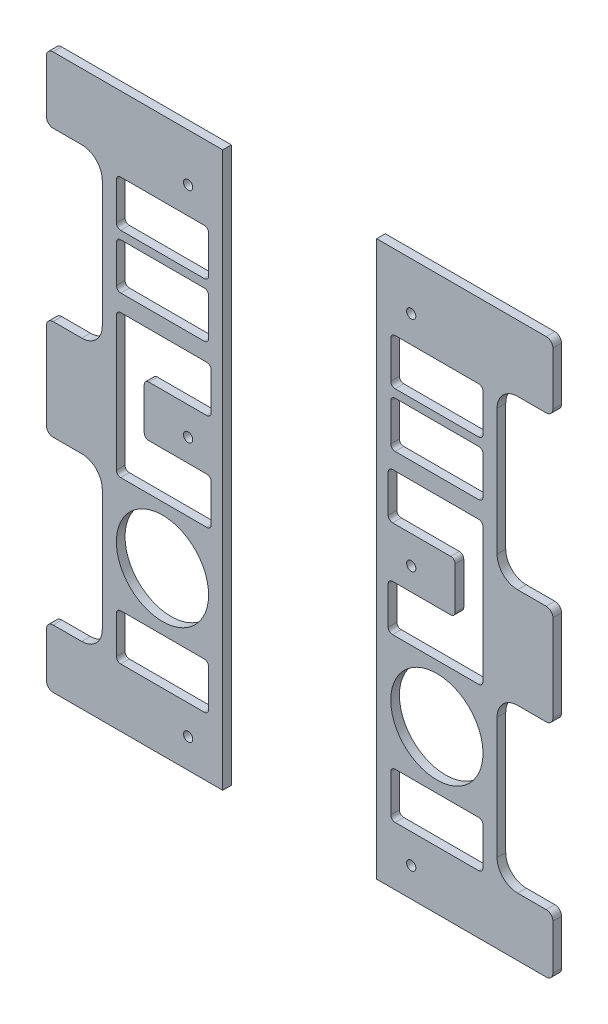
SolidWorks part; units mm, degrees
material "Acrylic (Medium-high impact)"
ref_plane "Front Plane" through (0, 0, 0) normal (0, 0, 1) x (1, 0, 0)
ref_plane "Top Plane" through (0, 0, 0) normal (0, 1, 0) x (1, 0, 0)
ref_plane "Right Plane" through (0, 0, 0) normal (1, 0, 0) x (0, 0, -1)
sketch "Sketch2" plane through (0, 0, 0) normal (0, 0, 1) x (1, 0, 0)
  line L1 (84.7976, -24.2496) -> (218.4211, -24.2496)
  line L2 (84.7976, -24.2496) -> (84.7976, -46.0935)
  line L4 (217.5275, -119.6519) -> (217.5275, -258.9871)
  line L7 (84.7976, -298.45) -> (84.7976, -342.4551)
  line L10 (84.7976, -46.0935) -> (84.7976, -298.45)
  line L11 (84.7976, -172.2717) -> (217.5275, -172.2717) construction
  line L13 (84.7976, -635.4166) -> (271.6317, -635.4166)
  line L14 (84.7976, -635.4166) -> (84.7976, -571.0484)
  line L17 (217.5275, -414.483) -> (217.5275, -548.4457)
  line L18 (84.7976, -342.4551) -> (84.7976, -571.0484)
  line L19 (151.1625, -172.2717) -> (151.1625, -456.7517) construction
  line L24 (84.7976, -456.7517) -> (151.1625, -456.7517) construction
  line L31 (278.9977, -628.0506) -> (278.9977, -578.4177)
  line L33 (278.9977, -606.7976) -> (278.9977, -675.1407) construction
  line L37 (278.9977, -288.878) -> (278.9977, -384.5922)
  line L38 (218.4211, -24.2496) -> (271.6723, -24.2496)
  line L40 (240.0929, -281.5526) -> (271.6723, -281.5526)
  line L41 (240.0929, -97.0864) -> (271.6723, -97.0864)
  line L42 (240.0929, -391.9176) -> (271.6723, -391.9176)
  line L43 (278.9977, -31.575) -> (278.9977, -89.761)
  line L45 (171.2551, -291.3572) -> (171.2551, -337.6663)
  line L47 (201.9625, -317.5) -> (201.9625, -357.5087)
  line L48 (166.4697, -342.4517) -> (102.282, -342.4517)
  line L49 (201.9625, -357.5087) -> (201.9625, -388.4663)
  line L50 (197.1771, -393.2517) -> (102.282, -393.2517)
  line L51 (97.4966, -347.2372) -> (97.4966, -388.4663)
  line L52 (166.4697, -286.5717) -> (102.282, -286.5717)
  line L53 (201.9625, -317.5) -> (201.9625, -240.5572)
  line L54 (197.1771, -235.7717) -> (102.282, -235.7717)
  line L55 (97.4966, -281.7863) -> (97.4966, -240.5572)
  line L56 (105.148, -520.2517) -> (197.1771, -520.2517)
  line L57 (100.3625, -525.0372) -> (100.3625, -566.2663)
  line L58 (105.148, -571.0517) -> (197.1771, -571.0517)
  line L59 (201.9625, -525.0372) -> (201.9625, -566.2663)
  line L60 (271.6317, -571.0517) -> (240.1335, -571.0517)
  line L61 (105.148, -166.2473) -> (197.1771, -166.2473)
  line L62 (100.3625, -171.0327) -> (100.3625, -212.2618)
  line L63 (105.148, -217.0473) -> (197.1771, -217.0473)
  line L64 (201.9625, -171.0327) -> (201.9625, -212.2618)
  line L65 (105.148, -106.4586) -> (197.1771, -106.4586)
  line L66 (100.3625, -111.2441) -> (100.3625, -152.4732)
  line L67 (105.148, -157.2586) -> (197.1771, -157.2586)
  line L68 (201.9625, -111.2441) -> (201.9625, -152.4732)
  circle A7 centre (151.1625, -456.7517) radius 50.8
  arc A8 (217.5275, -414.483) -> (240.0929, -391.9176) centre (240.0929, -414.483) cw
  circle A9 centre (122.8976, -317.5) radius 5.08 construction
  circle A10 centre (122.8976, -603.25) radius 5.08 construction
  circle A11 centre (122.8976, -76.7193) radius 5.08
  circle A12 centre (122.8976, -317.5) radius 5.08
  circle A13 centre (122.8976, -603.25) radius 5.08
  arc A15 (217.5275, -258.9871) -> (240.0929, -281.5526) centre (240.0929, -258.9871) ccw
  arc A16 (217.5275, -119.6519) -> (240.0929, -97.0864) centre (240.0929, -119.6519) cw
  arc A17 (102.282, -393.2517) -> (97.4966, -388.4663) centre (102.282, -388.4663) cw
  arc A18 (201.9625, -388.4663) -> (197.1771, -393.2517) centre (197.1771, -388.4663) cw
  arc A19 (201.9625, -240.5572) -> (197.1771, -235.7717) centre (197.1771, -240.5572) ccw
  arc A20 (102.282, -286.5717) -> (97.4966, -281.7863) centre (102.282, -281.7863) cw
  arc A21 (102.282, -235.7717) -> (97.4966, -240.5572) centre (102.282, -240.5572) ccw
  arc A22 (102.282, -342.4517) -> (97.4966, -347.2372) centre (102.282, -347.2372) ccw
  arc A23 (171.2551, -337.6663) -> (166.4697, -342.4517) centre (166.4697, -337.6663) cw
  arc A24 (166.4697, -286.5717) -> (171.2551, -291.3572) centre (166.4697, -291.3572) cw
  arc A25 (100.3625, -566.2663) -> (105.148, -571.0517) centre (105.148, -566.2663) ccw
  arc A26 (197.1771, -571.0517) -> (201.9625, -566.2663) centre (197.1771, -566.2663) ccw
  arc A27 (197.1771, -520.2517) -> (201.9625, -525.0372) centre (197.1771, -525.0372) cw
  arc A28 (105.148, -520.2517) -> (100.3625, -525.0372) centre (105.148, -525.0372) ccw
  arc A29 (271.6723, -391.9176) -> (278.9977, -384.5922) centre (271.6723, -384.5922) ccw
  arc A30 (271.6723, -281.5526) -> (278.9977, -288.878) centre (271.6723, -288.878) cw
  arc A31 (271.6723, -97.0864) -> (278.9977, -89.761) centre (271.6723, -89.761) ccw
  arc A32 (271.6723, -24.2496) -> (278.9977, -31.575) centre (271.6723, -31.575) cw
  arc A33 (240.1335, -571.0517) -> (217.5275, -548.4457) centre (240.1335, -548.4457) cw
  arc A34 (271.6317, -635.4166) -> (278.9977, -628.0506) centre (271.6317, -628.0506) ccw
  arc A35 (278.9977, -578.4177) -> (271.6317, -571.0517) centre (271.6317, -578.4177) ccw
  arc A36 (100.3625, -212.2618) -> (105.148, -217.0473) centre (105.148, -212.2618) ccw
  arc A37 (197.1771, -217.0473) -> (201.9625, -212.2618) centre (197.1771, -212.2618) ccw
  arc A38 (197.1771, -166.2473) -> (201.9625, -171.0327) centre (197.1771, -171.0327) cw
  arc A39 (105.148, -166.2473) -> (100.3625, -171.0327) centre (105.148, -171.0327) ccw
  arc A40 (100.3625, -152.4732) -> (105.148, -157.2586) centre (105.148, -152.4732) ccw
  arc A41 (197.1771, -157.2586) -> (201.9625, -152.4732) centre (197.1771, -152.4732) ccw
  arc A42 (197.1771, -106.4586) -> (201.9625, -111.2441) centre (197.1771, -111.2441) cw
  arc A43 (105.148, -106.4586) -> (100.3625, -111.2441) centre (105.148, -111.2441) ccw
  point P47 (217.5275, -571.0517)
  point P51 (278.9977, -635.4166)
  point P64 (97.4966, -393.2517)
  point P71 (97.4966, -286.5717)
  point P74 (97.4966, -235.7717)
  point P77 (97.4966, -342.4517)
  point P80 (171.2551, -342.4517)
  point P83 (171.2551, -286.5717)
  point P91 (201.9625, -571.0517)
  point P94 (201.9625, -520.2517)
  point P97 (151.1625, -520.2517)
  point P100 (278.9977, -391.9176)
  point P104 (278.9977, -281.5526)
  point P108 (278.9977, -97.0864)
  point P118 (151.1625, -157.2586)
  point P131 (151.1625, -166.2473)
  dimension "D4" = 22.5654
  dimension "D6" = 12.7
  dimension "D2" = 22.5654
  dimension "D17" = 4.7854
  dimension "D20" = 4.7854
  dimension "D21" = 7.3254
  dimension "D3" = 22.606
  dimension "D7" = 7.366
  dimension "D13" = 50.8
  dimension "D14" = 50.8
  dimension "D16" = 55.88
  dimension "D18" = 12.7
  dimension "D19" = 50.8
extrude "Boss-Extrude1" add sketch "Sketch2" along normal up to surface (9.525 mm away)
mirror "Mirror4" about plane through (0, 0, 0) normal (1, 0, 0) of bodies 106
